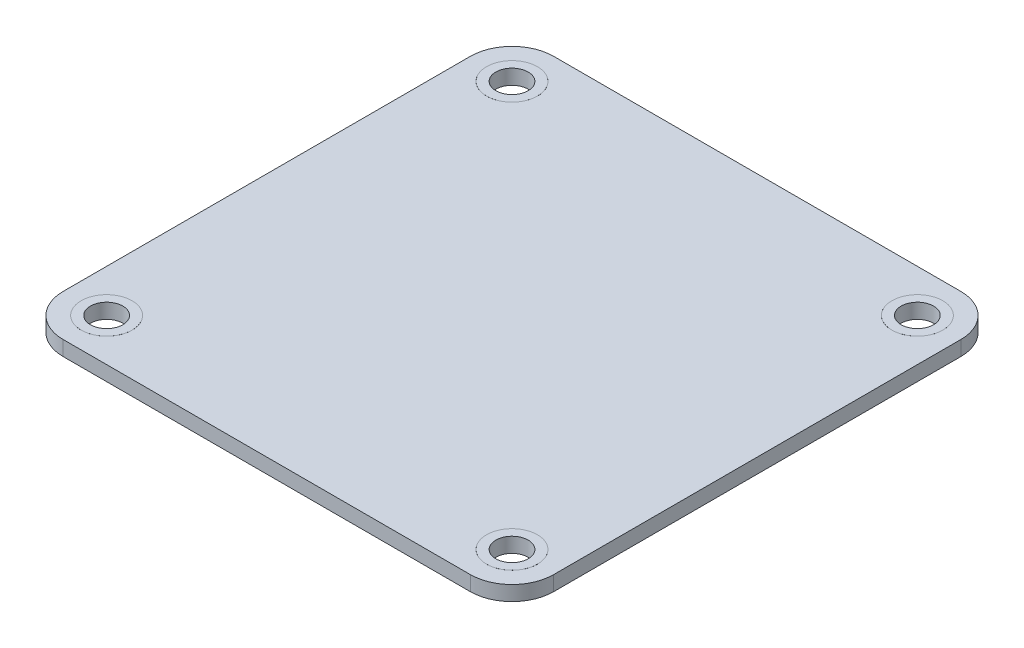
SolidWorks part; units mm, degrees
material "E-Glass Fiber"
ref_plane "Front Plane" through (0, 0, 0) normal (0, 0, 1) x (1, 0, 0)
ref_plane "Top Plane" through (0, 0, 0) normal (0, 1, 0) x (1, 0, 0)
ref_plane "Right Plane" through (0, 0, 0) normal (1, 0, 0) x (0, 0, -1)
sketch "Sketch1" plane through (0, 0, 0) normal (0, 1, 0) x (1, 0, 0)
  line L1 (22, -26.5) -> (-22, -26.5)
  line L2 (26.5, -22) -> (26.5, 22)
  line L3 (22, 26.5) -> (-22, 26.5)
  line L4 (-26.5, -22) -> (-26.5, 22)
  line L5 (26.5, -26.5) -> (-26.5, 26.5) construction
  line L6 (26.5, 26.5) -> (-26.5, -26.5) construction
  circle A0 centre (-21.9, 21.9) radius 1.755
  circle A1 centre (21.9, 21.9) radius 1.755
  circle A2 centre (-21.9, -21.9) radius 1.755
  circle A3 centre (21.9, -21.9) radius 1.755
  arc A4 (-26.5, 22) -> (-22, 26.5) centre (-22, 22) cw
  arc A5 (22, 26.5) -> (26.5, 22) centre (22, 22) cw
  arc A6 (26.5, -22) -> (22, -26.5) centre (22, -22) cw
  arc A7 (-22, -26.5) -> (-26.5, -22) centre (-22, -22) cw
  point P0 (0, 0)
  dimension "D3" = 3.51
  dimension "D5" = 4.5
  dimension "D1" = 53
  dimension "D2" = 53
  dimension "D4" = 43.8
extrude "Boss-Extrude1" add sketch "Sketch1" along normal blind 1.6
sketch "Sketch2" plane through (0, 0, 0) normal (0, 1, 0) x (1, 0, 0)
  circle A0 centre (-21.9, 21.9) radius 2.75
  circle A1 centre (21.9, 21.9) radius 2.75
  circle A2 centre (21.9, -21.9) radius 2.75
  circle A3 centre (-21.9, -21.9) radius 2.75
  circle A4 centre (-21.9, 21.9) radius 1.75
  circle A5 centre (21.9, 21.9) radius 1.75
  circle A6 centre (21.9, -21.9) radius 1.75
  circle A7 centre (-21.9, -21.9) radius 1.75
  dimension "D1" = 5.5
  dimension "D2" = 3.5
extrude "Boss-Extrude2" add sketch "Sketch2" along normal mid plane 1.61 from offset 0.8
